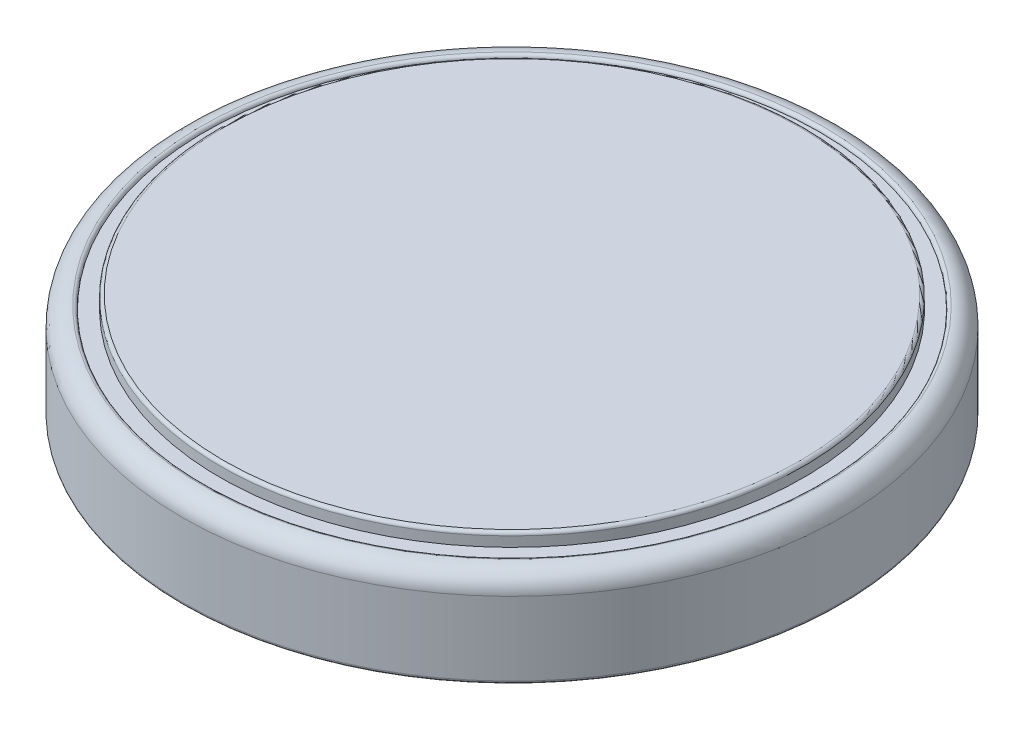
SolidWorks part; units mm, degrees
ref_plane "Front Plane" through (0, 0, 0) normal (0, 0, 1) x (1, 0, 0)
ref_plane "Top Plane" through (0, 0, 0) normal (0, 1, 0) x (1, 0, 0)
ref_plane "Right Plane" through (0, 0, 0) normal (1, 0, 0) x (0, 0, -1)
sketch "Sketch1" plane through (0, 0, 0) normal (0, 0, 1) x (1, 0, 0)
  line L0 (0, 0) -> (10, 0)
  line L1 (10, 0) -> (10, 2.325)
  line L2 (0, 0) -> (0, 3.2)
  line L3 (0, 3.2) -> (8.75, 3.2)
  line L4 (8.85, 3.1) -> (8.85, 2.8)
  line L5 (8.85, 2.8) -> (9.425, 2.8) construction
  line L6 (9.425, 2.8) -> (9.425, 2.9) construction
  line L7 (9.425, 2.8) -> (10, 2.8) construction
  line L8 (10, 2.8) -> (10, 2.325) construction
  line L9 (8.85, 2.8) -> (9.325, 2.8)
  arc A0 (10, 2.325) -> (9.425, 2.9) centre (9.425, 2.325) ccw
  arc A1 (9.425, 2.9) -> (9.325, 2.8) centre (9.425, 2.8) ccw
  arc A2 (8.75, 3.2) -> (8.85, 3.1) centre (8.75, 3.1) cw
  point P14 (8.85, 3.2)
  dimension "D5" = 0.1
  dimension "D6" = 0.1
  dimension "D1" = 3.2
  dimension "D2" = 10
  dimension "D3" = 8.85
  dimension "D4" = 2.9
revolve "Revolve1" add sketch "Sketch1" angle 360 about L2
fillet "Fillet1" radius 0.1 1 edges at (0, 0, -10)
